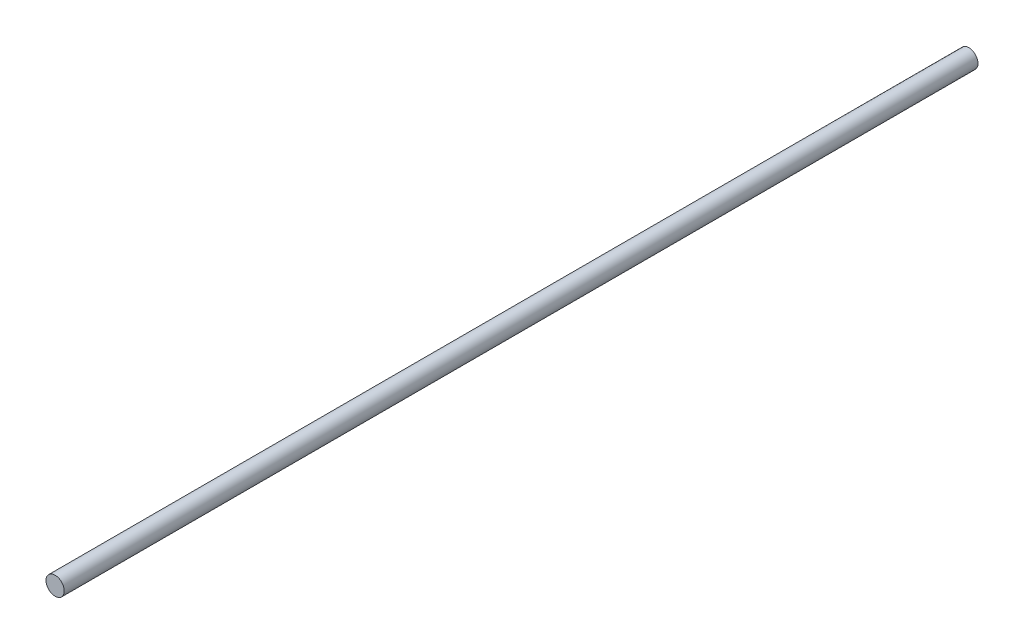
SolidWorks part; units mm, degrees
ref_plane "Front Plane" through (0, 0, 0) normal (0, 0, 1) x (1, 0, 0)
ref_plane "Top Plane" through (0, 0, 0) normal (0, 1, 0) x (1, 0, 0)
ref_plane "Right Plane" through (0, 0, 0) normal (1, 0, 0) x (0, 0, -1)
sketch "Sketch1" plane through (0, 0, 0) normal (0, 0, 1) x (1, 0, 0)
  circle A0 centre (0, 0) radius 1
extrude "Boss-Extrude1" add sketch "Sketch1" along normal blind 100
